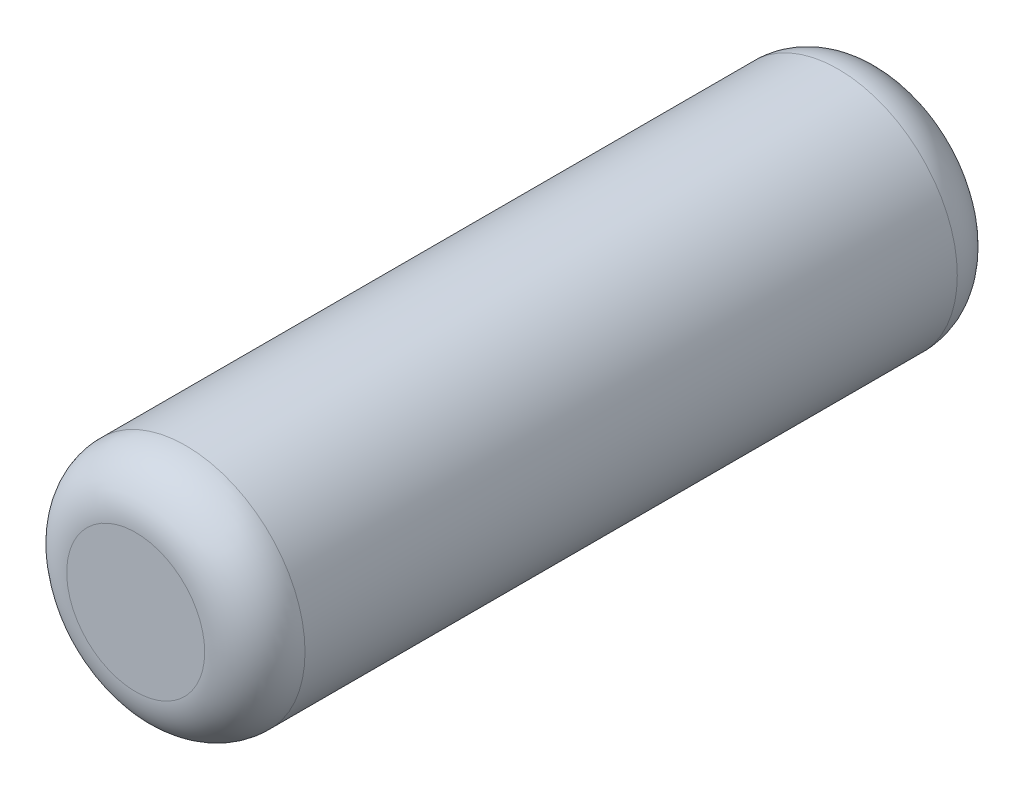
SolidWorks part; units mm, degrees
material "Nylon 101"
ref_plane "Front Plane" through (0, 0, 0) normal (0, 0, 1) x (1, 0, 0)
ref_plane "Top Plane" through (0, 0, 0) normal (0, 1, 0) x (1, 0, 0)
ref_plane "Right Plane" through (0, 0, 0) normal (1, 0, 0) x (0, 0, -1)
sketch "Sketch1" plane through (0, 0, 0) normal (0, 0, 1) x (1, 0, 0)
  circle A0 centre (0, 0) radius 120.65
  dimension "D1" = 241.3
extrude "Boss-Extrude1" add sketch "Sketch1" along normal blind 762 contours A0
fillet "Fillet2" radius 50.8 2 edges at (120.65, 0, 0) (120.65, 0, 762)
sketch "Sketch2" plane through (0, 0, 762) normal (0, 0, 1) x (1, 0, 0)
  circle A0 centre (0, 0) radius 101.6
  dimension "D1" = 203.2
extrude "Cut-Extrude1" cut sketch "Sketch2" against normal blind 711.2 from offset 25.4
